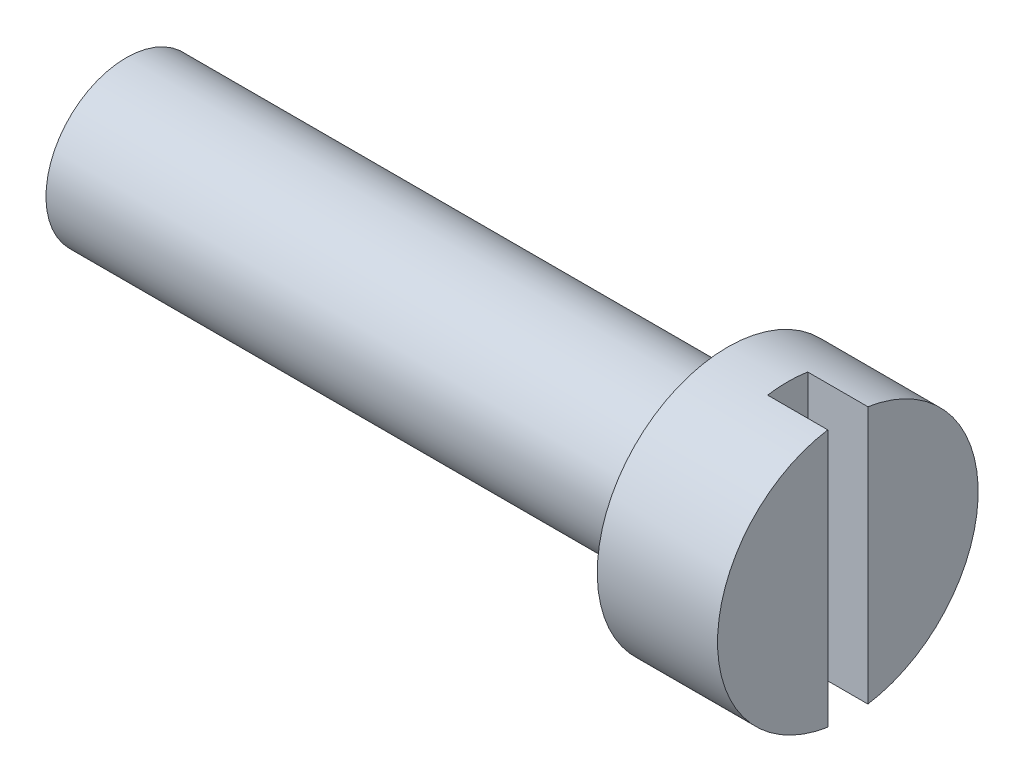
SolidWorks part; units mm, degrees
material "AISI 316 Stainless Steel Sheet (SS)"
ref_plane "Front Plane" through (0, 0, 0) normal (0, 0, 1) x (1, 0, 0)
ref_plane "Top Plane" through (0, 0, 0) normal (0, 1, 0) x (1, 0, 0)
ref_plane "Right Plane" through (0, 0, 0) normal (1, 0, 0) x (0, 0, -1)
sketch "Sketch1" plane through (0, 0, 0) normal (0, 0, 1) x (1, 0, 0)
  line L0 (0, 0) -> (-18, 0)
  line L1 (-18, 0) -> (-18, 2)
  line L2 (-18, 2) -> (-3, 2)
  line L3 (-3, 2) -> (-3, 3.25)
  line L4 (-3, 3.25) -> (0, 3.25)
  line L5 (0, 3.25) -> (0, 0)
  dimension "D1" = 3
  dimension "D2" = 15
  dimension "D3" = 2
  dimension "D4" = 3.25
revolve "Revolve1" add sketch "Sketch1" angle 360 about L0
sketch "Sketch2" plane through (0, 0, 0) normal (1, 0, 0) x (0, 0, -1)
  line L1 (-0.5, -3.25) -> (0.5, -3.25)
  line L2 (-0.5, -3.25) -> (-0.5, 3.25)
  line L3 (-0.5, 3.25) -> (0.5, 3.25)
  line L4 (0.5, -3.25) -> (0.5, 3.25)
  line L5 (-0.5, -3.25) -> (0.5, 3.25) construction
  line L6 (-0.5, 3.25) -> (0.5, -3.25) construction
  circle A0 centre (0, 0) radius 3.25 construction
  point P0 (0, 0)
  dimension "D1" = 1
extrude "Cut-Extrude1" cut sketch "Sketch2" against normal blind 1.5
